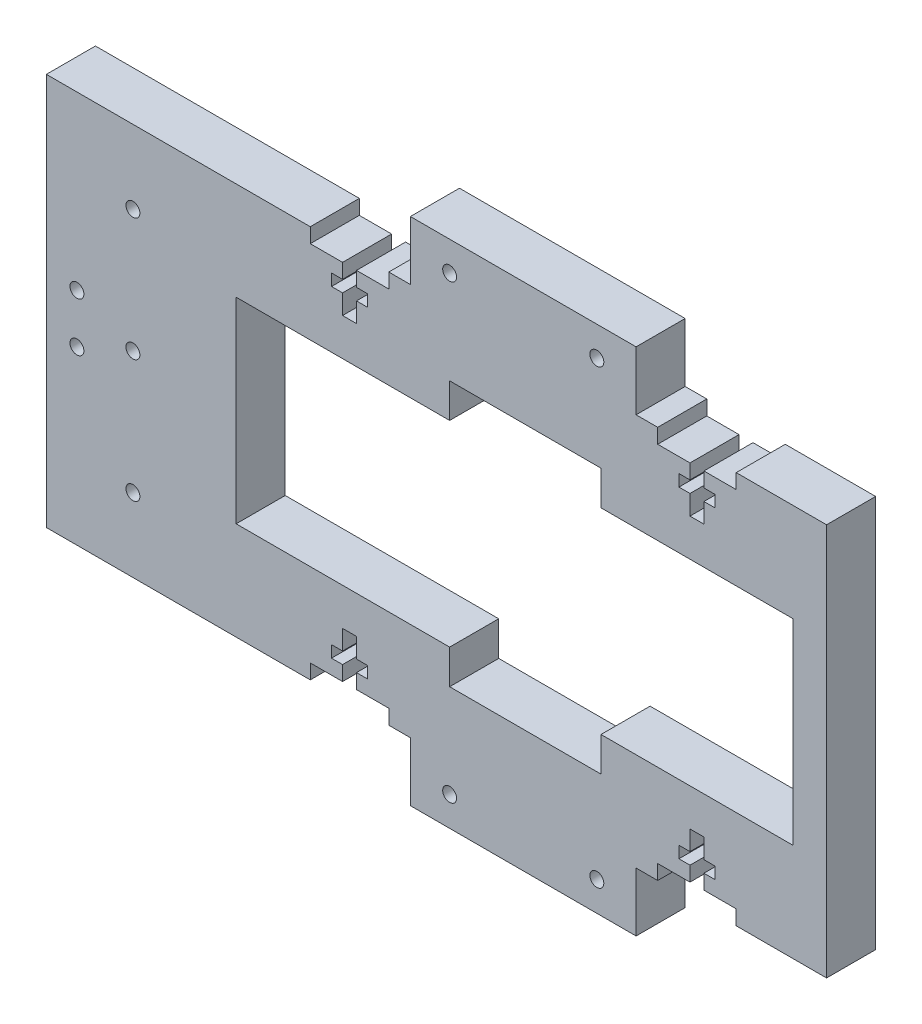
SolidWorks part; units mm, degrees
ref_plane "Front Plane" through (0, 0, 0) normal (0, 0, 1) x (1, 0, 0)
ref_plane "Top Plane" through (0, 0, 0) normal (0, 1, 0) x (1, 0, 0)
ref_plane "Right Plane" through (0, 0, 0) normal (1, 0, 0) x (0, 0, -1)
sketch "Sketch1" plane through (0, 0, 0) normal (0, 0, 1) x (1, 0, 0)
  line L0 (109, 80) -> (109, 77)
  line L1 (0, 0) -> (38.1871, 0)
  line L2 (143.4175, 20) -> (143.4175, 0)
  line L3 (5, 80) -> (38.1871, 80)
  line L4 (58.5936, 80) -> (58.5936, 92)
  line L5 (109, 77) -> (115.58, 77)
  line L6 (118.42, 71.61) -> (118.42, 67.61)
  line L7 (118.42, 77) -> (118.42, 74)
  line L8 (118.42, 67.61) -> (115.58, 67.61)
  line L9 (115.58, 71.61) -> (115.58, 67.61)
  line L10 (120.67, 71.61) -> (118.42, 71.61)
  line L11 (113.33, 74) -> (115.58, 74)
  line L12 (113.33, 74) -> (113.33, 71.61)
  line L13 (113.33, 71.61) -> (115.58, 71.61)
  line L14 (120.67, 74) -> (120.67, 71.61)
  line L15 (120.67, 74) -> (118.42, 74)
  line L16 (115.58, 77) -> (115.58, 74)
  line L17 (125, 77) -> (118.42, 77)
  line L18 (125, 80) -> (125, 77)
  line L19 (125, 80) -> (143.4175, 80)
  line L20 (247.4135, 40) -> (-51.1789, 40) construction
  line L21 (109, 0) -> (109, 3)
  line L22 (109, 3) -> (115.58, 3)
  line L23 (115.58, 3) -> (115.58, 6)
  line L24 (113.33, 6) -> (115.58, 6)
  line L25 (113.33, 6) -> (113.33, 8.39)
  line L26 (113.33, 8.39) -> (115.58, 8.39)
  line L27 (115.58, 8.39) -> (115.58, 12.39)
  line L28 (118.42, 12.39) -> (115.58, 12.39)
  line L29 (118.42, 8.39) -> (118.42, 12.39)
  line L30 (120.67, 8.39) -> (118.42, 8.39)
  line L31 (120.67, 6) -> (120.67, 8.39)
  line L32 (120.67, 6) -> (118.42, 6)
  line L33 (118.42, 3) -> (118.42, 6)
  line L34 (125, 3) -> (118.42, 3)
  line L35 (125, 0) -> (125, 3)
  line L36 (143.4175, 60) -> (143.4175, 80)
  line L37 (143.4175, 0) -> (125, 0)
  line L38 (58.5936, 92) -> (104.5936, 92)
  line L39 (104.5936, 92) -> (104.5936, 80)
  line L40 (58.5936, 0) -> (58.5936, -12)
  line L41 (58.5936, -12) -> (104.5936, -12)
  line L42 (104.5936, -12) -> (104.5936, 0)
  line L43 (104.5936, 80) -> (109, 80)
  line L44 (104.5936, 0) -> (109, 0)
  line L45 (5, 80) -> (-15.6021, 80)
  line L46 (136.6006, 60) -> (136.6006, 20)
  line L47 (-15.6021, 0) -> (0, 0)
  line L48 (81.5936, -22.2503) -> (81.5936, 103.8754) construction
  line L49 (54.1871, 0) -> (54.1871, 3)
  line L50 (54.1871, 3) -> (47.6071, 3)
  line L51 (44.7671, 12.39) -> (47.6071, 12.39)
  line L52 (47.6071, 8.39) -> (47.6071, 12.39)
  line L53 (49.8571, 8.39) -> (47.6071, 8.39)
  line L54 (49.8571, 6) -> (49.8571, 8.39)
  line L55 (49.8571, 6) -> (47.6071, 6)
  line L56 (47.6071, 3) -> (47.6071, 6)
  line L57 (38.1871, 0) -> (38.1871, 3)
  line L58 (38.1871, 3) -> (44.7671, 3)
  line L59 (44.7671, 3) -> (44.7671, 6)
  line L60 (42.5171, 6) -> (44.7671, 6)
  line L61 (42.5171, 6) -> (42.5171, 8.39)
  line L62 (42.5171, 8.39) -> (44.7671, 8.39)
  line L63 (44.7671, 8.39) -> (44.7671, 12.39)
  line L64 (58.5936, 80) -> (54.1871, 80)
  line L65 (54.1871, 80) -> (54.1871, 77)
  line L66 (54.1871, 77) -> (47.6071, 77)
  line L67 (49.8571, 71.61) -> (47.6071, 71.61)
  line L68 (49.8571, 74) -> (49.8571, 71.61)
  line L69 (49.8571, 74) -> (47.6071, 74)
  line L70 (47.6071, 77) -> (47.6071, 74)
  line L71 (38.1871, 80) -> (38.1871, 77)
  line L72 (38.1871, 77) -> (44.7671, 77)
  line L73 (44.7671, 77) -> (44.7671, 74)
  line L74 (42.5171, 74) -> (44.7671, 74)
  line L75 (42.5171, 74) -> (42.5171, 71.61)
  line L76 (42.5171, 71.61) -> (44.7671, 71.61)
  line L77 (47.6071, 71.61) -> (47.6071, 67.61)
  line L78 (44.7671, 67.61) -> (47.6071, 67.61)
  line L79 (44.7671, 71.61) -> (44.7671, 67.61)
  line L80 (23.079, 60) -> (66.5936, 60)
  line L81 (54.1871, 0) -> (58.5936, 0)
  line L82 (23.079, 60) -> (23.079, 20)
  line L83 (23.079, 20) -> (66.5936, 20)
  line L84 (97.4428, 60) -> (136.6006, 60)
  line L85 (66.5936, 67) -> (97.4428, 67)
  line L86 (66.5936, 67) -> (66.5936, 60)
  line L87 (66.5936, 13) -> (97.4428, 13)
  line L88 (97.4428, 67) -> (97.4428, 60)
  line L89 (97.4428, 20) -> (136.6006, 20)
  line L90 (97.4428, 20) -> (97.4428, 13)
  line L91 (66.5936, 20) -> (66.5936, 13)
  line L92 (-15.6021, 80) -> (-15.6021, 0)
  line L93 (143.4175, 60) -> (143.4175, 20)
  circle A0 centre (2.0378, 40) radius 1.42
  circle A1 centre (2.0378, 65) radius 1.42
  circle A2 centre (2.0378, 15) radius 1.42
  circle A3 centre (66.5936, 86) radius 1.42
  circle A4 centre (96.5936, 86) radius 1.42
  circle A5 centre (96.5936, -6) radius 1.42
  circle A6 centre (66.5936, -6) radius 1.42
  circle A9 centre (-9.3748, 45) radius 1.42
  circle A10 centre (-9.3748, 35) radius 1.42
  point P19 (117, 67.61)
  dimension "D3" = 2.84
  dimension "D6" = 2.84
  dimension "D7" = 2.84
  dimension "D11" = 2.84
  dimension "D2" = 20
  dimension "D14" = 2.84
  dimension "D10" = 2.84
  dimension "D4" = 25
  dimension "D5" = 25
  dimension "D8" = 20
  dimension "D9" = 4
  dimension "D13" = 5
extrude "Boss-Extrude1" add sketch "Sketch1" along normal blind 10
